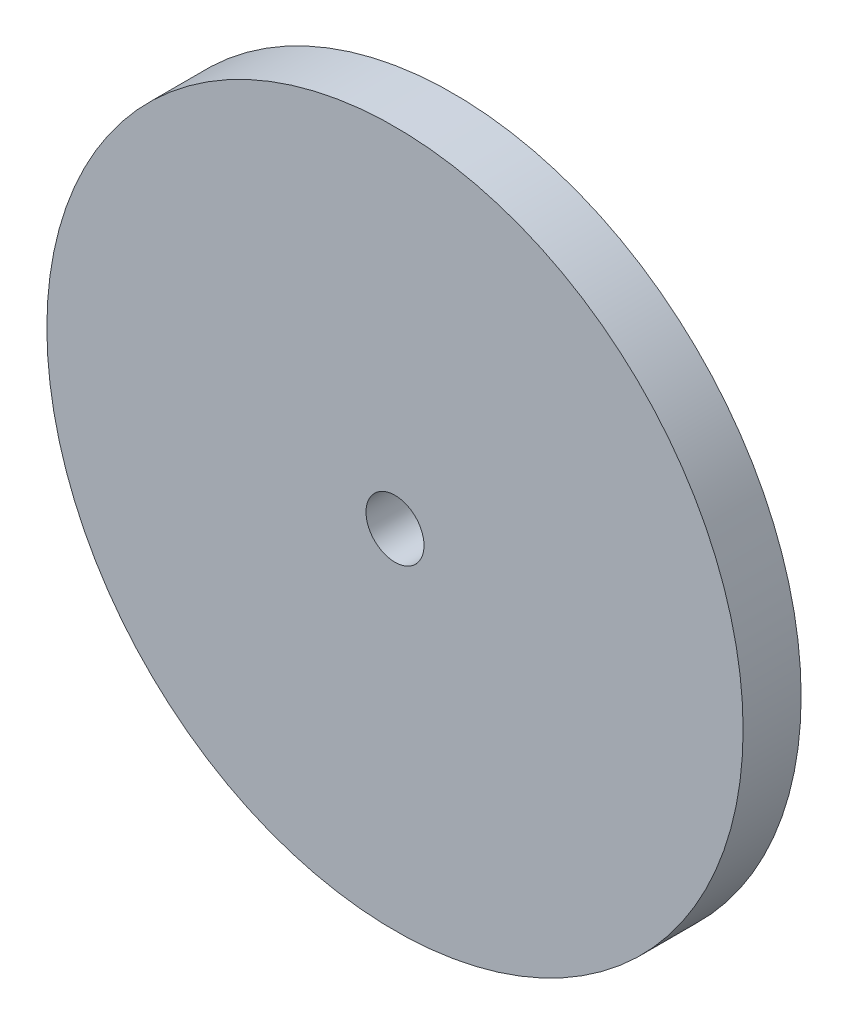
SolidWorks part; units mm, degrees
material "Oak"
ref_plane "Front" through (0, 0, 0) normal (0, 0, 1) x (1, 0, 0)
ref_plane "Top" through (0, 0, 0) normal (0, 1, 0) x (1, 0, 0)
ref_plane "Right" through (0, 0, 0) normal (1, 0, 0) x (0, 0, -1)
sketch "Sketch1" plane through (0, 0, 0) normal (0, 0, 1) x (1, 0, 0)
  circle A0 centre (0, 0) radius 38.1
  circle A1 centre (0, 0) radius 3.175
  dimension "D1" = 76.2
  dimension "D2" = 6.35
extrude "Boss-Extrude1" add sketch "Sketch1" along normal blind 6.35
